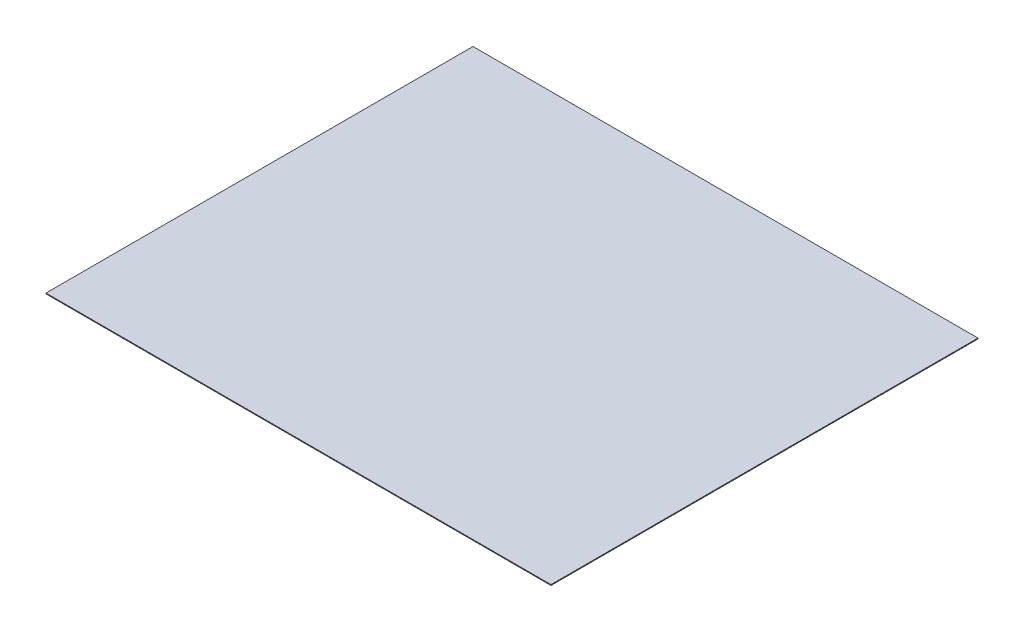
SolidWorks part; units mm, degrees
ref_plane "Front Plane" through (0, 0, 0) normal (0, 0, 1) x (1, 0, 0)
ref_plane "Top Plane" through (0, 0, 0) normal (0, 1, 0) x (1, 0, 0)
ref_plane "Right Plane" through (0, 0, 0) normal (1, 0, 0) x (0, 0, -1)
sketch "Sketch1" plane through (0, 0, 0) normal (0, 1, 0) x (1, 0, 0)
  line L1 (-320.5, 271) -> (320.5, 271)
  line L2 (-320.5, 271) -> (-320.5, -271)
  line L3 (-320.5, -271) -> (320.5, -271)
  line L4 (320.5, 271) -> (320.5, -271)
  line L5 (-320.5, 271) -> (320.5, -271) construction
  line L6 (-320.5, -271) -> (320.5, 271) construction
  point P0 (0, 0)
  dimension "D1" = 542
  dimension "D2" = 641
extrude "Boss-Extrude1" add sketch "Sketch1" along normal blind 1
